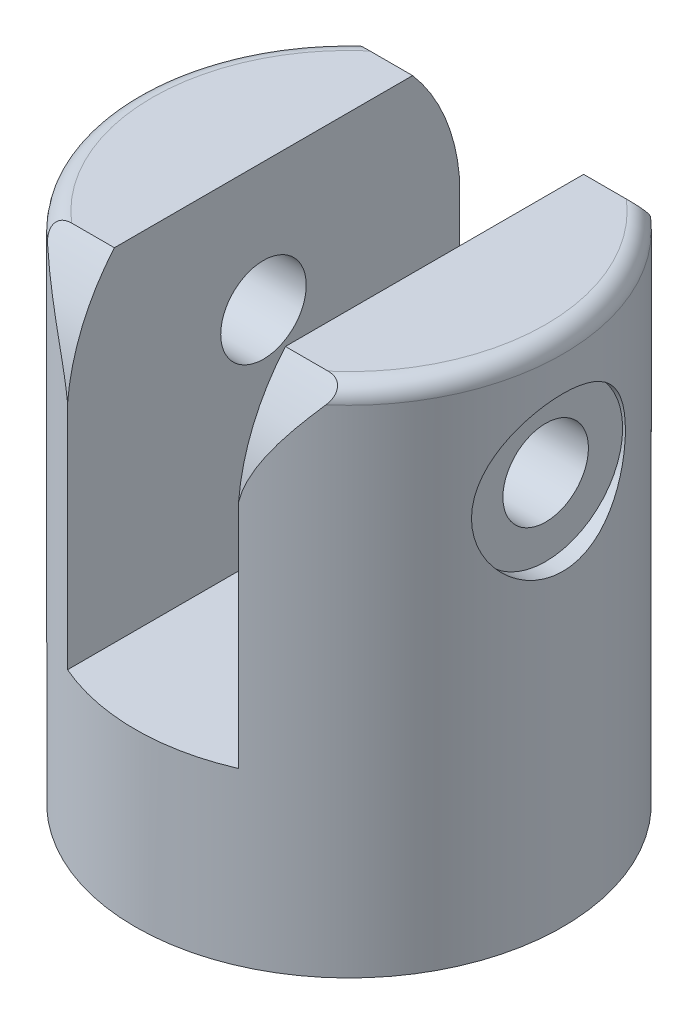
SolidWorks part; units mm, degrees
ref_plane "Front Plane" through (0, 0, 0) normal (0, 0, 1) x (1, 0, 0)
ref_plane "Top Plane" through (0, 0, 0) normal (0, 1, 0) x (1, 0, 0)
ref_plane "Right Plane" through (0, 0, 0) normal (1, 0, 0) x (0, 0, -1)
sketch "Sketch1" plane through (0, 0, 0) normal (0, 1, 0) x (1, 0, 0)
  circle A0 centre (0, 0) radius 125
  dimension "D1" = 250
extrude "Boss-Extrude1" add sketch "Sketch1" along normal blind 300
sketch "Sketch2" plane through (0, 300, 0) normal (0, 1, 0) x (1, 0, 0)
  line L1 (-50, 125) -> (50, 125)
  line L2 (-50, 125) -> (-50, -125)
  line L3 (-50, -125) -> (50, -125)
  line L4 (50, 125) -> (50, -125)
  line L5 (-50, 125) -> (50, -125) construction
  line L6 (-50, -125) -> (50, 125) construction
  circle A0 centre (0, 0) radius 125 construction
  point P0 (0, 0)
  dimension "D1" = 100
extrude "Cut-Extrude1" cut sketch "Sketch2" against normal blind 200
sketch "Sketch3" plane through (-50, 0, 0) normal (1, 0, 0) x (0, 0, -1)
  line L0 (114.5644, 300) -> (-114.5644, 300) construction
  line L1 (114.5644, 100) -> (-114.5644, 100) construction
  line L2 (-114.5644, 100) -> (114.5644, 100)
  line L3 (114.5644, 100) -> (114.5644, 300)
  line L4 (114.5644, 300) -> (-114.5644, 300)
  line L5 (-114.5644, 300) -> (-114.5644, 100)
  circle A0 centre (0, 225) radius 30
  circle A1 centre (0, 100) radius 114.5644
  dimension "D2" = 60
  dimension "D1" = 75
sketch "Sketch4" plane through (0, 0, 0) normal (0, -1, 0) x (1, 0, 0)
  circle A0 centre (0, 0) radius 50
  dimension "D1" = 100
extrude "Cut-Extrude3" cut sketch "Sketch4" against normal blind 60
ref_plane "Plane1" through (-125, 0, 0) normal (1, 0, 0) x (0, 0, -1)
ref_plane "Plane2" through (125, 0, 0) normal (-1, 0, 0) x (0, 0, 1)
sketch "Sketch7" plane through (-50, 0, 0) normal (1, 0, 0) x (0, 0, -1)
  line L0 (114.5644, 300) -> (-114.5644, 300) construction
  line L1 (-115, 225) -> (-114.5644, 300)
  line L2 (-114.5644, 300) -> (114.5644, 300)
  line L3 (114.5644, 300) -> (115, 225)
  circle A0 centre (0, 225) radius 25
  circle A1 centre (0, 225) radius 115
  line M1 (114.5644, 300) -> (-114.5644, 300)
  line M2 (-114.5644, 300) -> (-114.5644, 100)
  line M4 (114.5644, 100) -> (114.5644, 300)
  dimension "D2" = 50
  dimension "D1" = 75
  dimension "D3" = 90
extrude "Cut-Extrude6" cut sketch "Sketch7" against normal through all both and the other way through all contours A1 M1 M2 | A1 M4 M1 | A0
fillet "Fillet2" radius 10 4 edges at (125, 300, 0) (-58.2596, 256.5307, 110.593) (-125, 300, 0) (64.1952, 266.4853, -107.2566)
ref_plane "Plane3" through (-125, 0, 0) normal (1, 0, 0) x (0, 0, -1)
sketch "Sketch8" plane through (-125, 0, 0) normal (1, 0, 0) x (0, 0, -1)
  circle A0 centre (0, 225) radius 45
  circle A1 centre (0, 225) radius 25 construction
  circle A2 centre (0, 225) radius 25
  dimension "D1" = 20
extrude "Cut-Extrude7" cut sketch "Sketch8" along normal blind 10
ref_plane "Plane4" through (125, 0, 0) normal (-1, 0, 0) x (0, 0, 1)
sketch "Sketch10" plane through (125, 0, 0) normal (-1, 0, 0) x (0, 0, 1)
  circle A0 centre (0, 225) radius 45
  circle A1 centre (0, 225) radius 25 construction
  circle A2 centre (0, 225) radius 25
  dimension "D1" = 20
extrude "Cut-Extrude8" cut sketch "Sketch10" along normal blind 10
